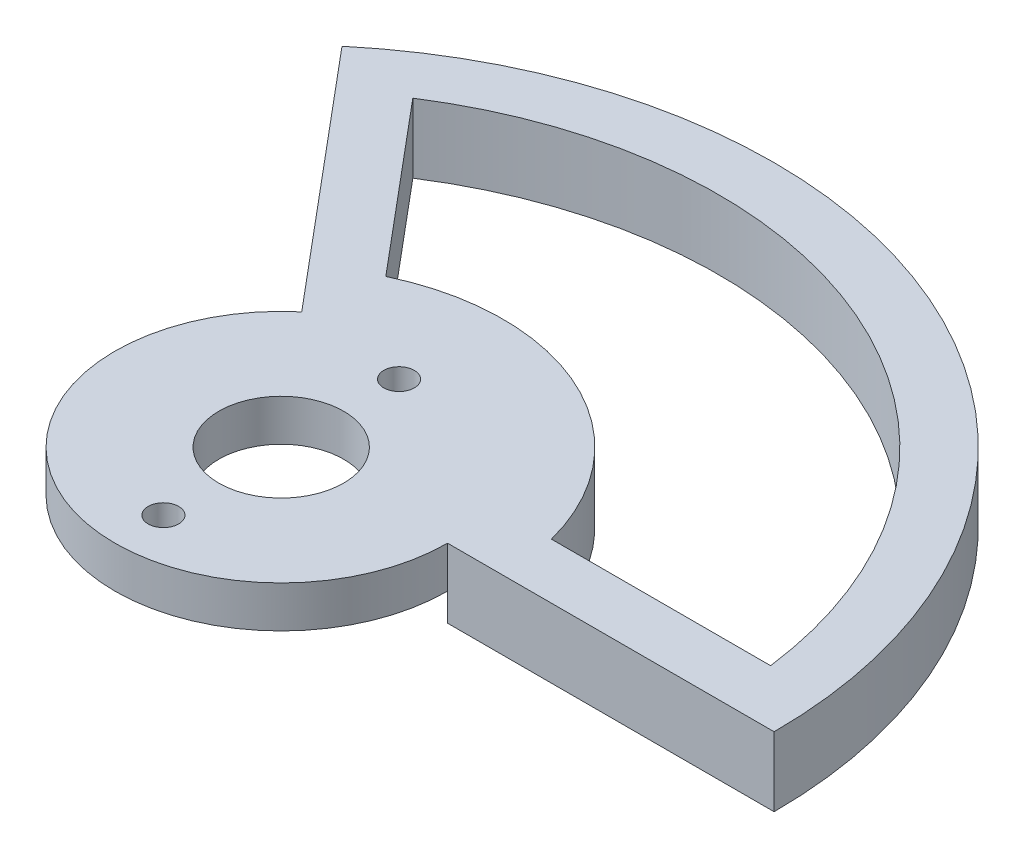
SolidWorks part; units mm, degrees
ref_plane "Front Plane" through (0, 0, 0) normal (0, 0, 1) x (1, 0, 0)
ref_plane "Top Plane" through (0, 0, 0) normal (0, 1, 0) x (1, 0, 0)
ref_plane "Right Plane" through (0, 0, 0) normal (1, 0, 0) x (0, 0, -1)
sketch "Sketch1" plane through (0, 0, 0) normal (0, 1, 0) x (1, 0, 0)
  circle A0 centre (0, 0) radius 4.5
  circle A1 centre (0, 0) radius 12
  circle A2 centre (0, 8.5) radius 1.1
  circle A3 centre (0, -8.5) radius 1.1
  dimension "D1" = 9
  dimension "D2" = 24
  dimension "D5" = 2.2
  dimension "D3" = 8.5
  dimension "D4" = 8.5
extrude "Boss-Extrude1" add sketch "Sketch1" along normal blind 3
sketch "Sketch2" plane through (0, 3, 0) normal (0, 1, 0) x (1, 0, 0)
  line L0 (0, 0) -> (35.56, 0) construction
  line L1 (12, 0) -> (35.56, 0)
  line L2 (-22.8575, 27.2405) -> (-7.7135, 9.1925)
  circle A0 centre (0, 0) radius 12 construction
  arc A1 (12, 0) -> (-7.7135, 9.1925) centre (0, 0) ccw
  arc A2 (35.56, 0) -> (-22.8575, 27.2405) centre (0, 0) ccw
  dimension "D1" = 35.56
  dimension "D2" = 230
extrude "Boss-Extrude2" add sketch "Sketch2" against normal blind 5
sketch "Sketch3" plane through (0, -2, 0) normal (0, -1, 0) x (1, 0, 0)
  line L4 (31.3055, -4) -> (15.4919, -4)
  line L5 (-6.8938, -14.4387) -> (-17.0586, -26.5525)
  line L6 (31.3055, -4) -> (15.4919, -4)
  line L7 (-6.8938, -14.4387) -> (-17.0586, -26.5525)
  arc A4 (-17.0586, -26.5525) -> (31.3055, -4) centre (0, 0) ccw
  arc A5 (-6.8938, -14.4387) -> (15.4919, -4) centre (0, 0) ccw
  arc A6 (-17.0586, -26.5525) -> (31.3055, -4) centre (0, 0) ccw
  arc A7 (-6.8938, -14.4387) -> (15.4919, -4) centre (0, 0) ccw
  dimension "D1" = 4
extrude "Cut-Extrude1" cut sketch "Sketch3" against normal through all
